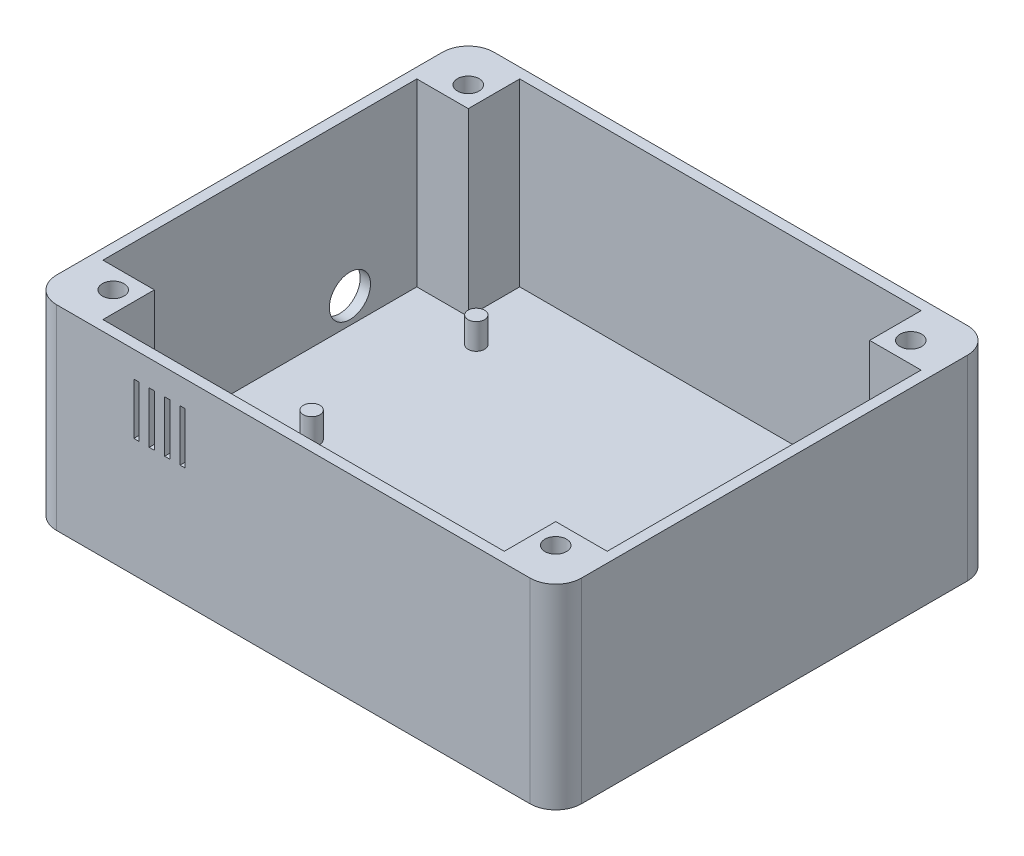
SolidWorks part; units mm, degrees
ref_plane "Front Plane" through (0, 0, 0) normal (0, 0, 1) x (1, 0, 0)
ref_plane "Top Plane" through (0, 0, 0) normal (0, 1, 0) x (1, 0, 0)
ref_plane "Right Plane" through (0, 0, 0) normal (1, 0, 0) x (0, 0, -1)
sketch "Sketch1" plane through (0, 0, 0) normal (0, 1, 0) x (1, 0, 0)
  line L0 (0, 0) -> (-28.5509, 0) construction
  line L1 (-51, 42.5) -> (51, 42.5)
  line L2 (-51, 42.5) -> (-51, -42.5)
  line L3 (-51, -42.5) -> (51, -42.5)
  line L4 (51, 42.5) -> (51, -42.5)
  line L5 (-51, 42.5) -> (51, -42.5) construction
  line L6 (-51, -42.5) -> (51, 42.5) construction
  line L7 (0, 0) -> (0, 21.5292) construction
  point P0 (0, 0)
  dimension "D1" = 102
  dimension "D2" = 85
extrude "Boss-Extrude1" add sketch "Sketch1" along normal blind 38 contours L2 L1 L4 L3
sketch "Sketch2" plane through (0, 38, 0) normal (0, 1, 0) x (1, 0, 0)
  line L0 (-39, 40.5) -> (39, 40.5)
  line L1 (39, 40.5) -> (39, 30.5)
  line L2 (39, 30.5) -> (49, 30.5)
  line L3 (49, 30.5) -> (49, -30.5)
  line L4 (49, -30.5) -> (39, -30.5)
  line L5 (39, -30.5) -> (39, -40.5)
  line L6 (39, -40.5) -> (-39, -40.5)
  line L7 (-39, -40.5) -> (-39, -30.5)
  line L8 (-39, -30.5) -> (-49, -30.5)
  line L9 (-49, -30.5) -> (-49, 30.5)
  line L10 (-49, 30.5) -> (-39, 30.5)
  line L11 (-39, 30.5) -> (-39, 40.5)
  line L12 (-51, 42.5) -> (51, 42.5) construction
  line L13 (51, 42.5) -> (51, -42.5) construction
  line L14 (-51, -42.5) -> (51, -42.5) construction
  line L15 (-51, 42.5) -> (-51, -42.5) construction
  circle A0 centre (43, 34.5) radius 2.1
  circle A1 centre (-43, -34.5) radius 2.1
  circle A2 centre (43, -34.5) radius 2.1
  dimension "D15" = 4.2
  dimension "D18" = 4.2
  dimension "D21" = 4.2
  dimension "D1" = 2
  dimension "D2" = 2
  dimension "D3" = 2
  dimension "D4" = 2
  dimension "D5" = 10
  dimension "D6" = 10
  dimension "D7" = 10
  dimension "D8" = 10
  dimension "D9" = 10
  dimension "D10" = 10
  dimension "D11" = 10
  dimension "D12" = 10
  dimension "D13" = 8
  dimension "D14" = 8
  dimension "D16" = 8
  dimension "D17" = 8
  dimension "D19" = 8
  dimension "D20" = 8
extrude "Cut-Extrude1" cut sketch "Sketch2" against normal blind 35
sketch "Sketch3" plane through (0, 38, 0) normal (0, 1, 0) x (1, 0, 0)
  line L0 (-51, 42.5) -> (51, 42.5) construction
  line L1 (-51, 42.5) -> (-51, -42.5) construction
  circle A0 centre (-43, 34.5) radius 2.1
  dimension "D3" = 4.2
  dimension "D1" = 8
  dimension "D2" = 8
extrude "Cut-Extrude2" cut sketch "Sketch3" against normal blind 35 contours A0
sketch "Sketch5" plane through (-51, 0, 0) normal (-1, 0, 0) x (0, 0, 1)
  line L0 (-42.5, 38) -> (-42.5, 0) construction
  line L1 (42.5, 38) -> (42.5, 0) construction
  circle A0 centre (-17.5, 7.9985) radius 4
  circle A1 centre (17.5, 7.9985) radius 4
  dimension "D1" = 25
  dimension "D2" = 25
extrude "Cut-Extrude4" cut sketch "Sketch5" against normal blind 10
fillet "Fillet1" radius 5 1 edges at (-51, 19, 42.5)
fillet "Fillet2" radius 5 1 edges at (-51, 19, -42.5)
fillet "Fillet3" radius 5 1 edges at (51, 19, 42.5)
fillet "Fillet4" radius 5 1 edges at (51, 19, -42.5)
sketch "Sketch6" plane through (0, 3, 0) normal (0, 1, 0) x (1, 0, 0)
  circle A0 centre (-33.5, 26.565) radius 1.6
  circle A1 centre (-33.5, -5.435) radius 1.6
  circle A2 centre (33.5, 26.565) radius 1.6
  circle A3 centre (33.5, -5.435) radius 1.6
  dimension "D4" = 3.2
  dimension "D5" = 3.2
  dimension "D6" = 3.2
  dimension "D7" = 3.2
  dimension "D1" = 32
  dimension "D2" = 67
extrude "Boss-Extrude2" add sketch "Sketch6" along normal blind 5
sketch "Sketch7" plane through (-51, 0, 0) normal (-1, 0, 0) x (0, 0, 1)
  line L0 (-37.5, 0) -> (37.5, 0) construction
  line L1 (7.5, 0) -> (-7.5, 0)
  line L2 (7.5, 0) -> (7.5, 4)
  line L3 (7.5, 4) -> (-7.5, 4)
  line L4 (-7.5, 0) -> (-7.5, 4)
  line L5 (7.5, 0) -> (-7.5, 4) construction
  line L6 (7.5, 4) -> (-7.5, 0) construction
  line L7 (-37.5, 38) -> (-37.5, 0) construction
  point P0 (0, 2)
  dimension "D1" = 4
  dimension "D2" = 0
  dimension "D3" = 37.5
  dimension "D4" = 15
extrude "Boss-Extrude3" add sketch "Sketch7" along normal blind 12
chamfer "Chamfer1" distance 5 angle 45 1 edges at (-63, 2, -7.5)
chamfer "Chamfer2" distance 5 angle 45 1 edges at (-63, 2, 7.5)
sketch "Sketch8" plane through (0, 4, 0) normal (0, 1, 0) x (1, 0, 0)
  circle A0 centre (-56.6137, 0) radius 3.0123
extrude "Cut-Extrude5" cut sketch "Sketch8" against normal blind 5
fillet "Fillet5" radius 2 1 edges at (-58, 2, -7.5)
fillet "Fillet6" radius 2 1 edges at (-63, 2, -2.5)
fillet "Fillet7" radius 2 1 edges at (-63, 2, 2.5)
fillet "Fillet8" radius 2 1 edges at (-58, 2, 7.5)
sketch "Sketch9" plane through (0, 0, 42.5) normal (0, 0, 1) x (1, 0, 0)
  line L0 (-46, 38) -> (46, 38) construction
  line L1 (-30, 33) -> (-31, 33)
  line L2 (-30, 33) -> (-30, 23)
  line L3 (-30, 23) -> (-31, 23)
  line L4 (-31, 33) -> (-31, 23)
  line L5 (-30, 33) -> (-31, 23) construction
  line L6 (-30, 23) -> (-31, 33) construction
  line L7 (-46, 38) -> (-46, 0) construction
  point P0 (-30.5, 28)
  dimension "D1" = 10
  dimension "D2" = 1
  dimension "D3" = 5
  dimension "D4" = 15
extrude "Cut-Extrude6" cut sketch "Sketch9" against normal blind 2.1
sketch "Sketch10" plane through (0, 0, 42.5) normal (0, 0, 1) x (1, 0, 0)
  line L1 (-28, 33) -> (-27, 33)
  line L2 (-28, 33) -> (-28, 23)
  line L3 (-28, 23) -> (-27, 23)
  line L4 (-27, 33) -> (-27, 23)
  line L5 (-28, 33) -> (-27, 23) construction
  line L6 (-28, 23) -> (-27, 33) construction
  line L7 (-25, 33) -> (-24, 33)
  line L8 (-25, 33) -> (-25, 23)
  line L9 (-25, 23) -> (-24, 23)
  line L10 (-24, 33) -> (-24, 23)
  line L11 (-25, 33) -> (-24, 23) construction
  line L12 (-25, 23) -> (-24, 33) construction
  line L13 (-22, 33) -> (-21, 33)
  line L14 (-22, 33) -> (-22, 23)
  line L15 (-22, 23) -> (-21, 23)
  line L16 (-21, 33) -> (-21, 23)
  line L17 (-22, 33) -> (-21, 23) construction
  line L18 (-22, 23) -> (-21, 33) construction
  line L20 (-46, 38) -> (46, 38) construction
  line L21 (-30, 23) -> (-30, 33) construction
  point P0 (-27.5, 28)
  point P5 (-24.5, 28)
  point P10 (-21.5, 28)
  dimension "D1" = 10
  dimension "D2" = 10
  dimension "D3" = 10
  dimension "D4" = 1
  dimension "D5" = 1
  dimension "D6" = 1
  dimension "D7" = 5
  dimension "D8" = 5
  dimension "D9" = 5
  dimension "D10" = 2
  dimension "D11" = 2
  dimension "D12" = 2
extrude "Cut-Extrude7" cut sketch "Sketch10" against normal blind 2.1
equation "\"2.1.00mm\"=5"
